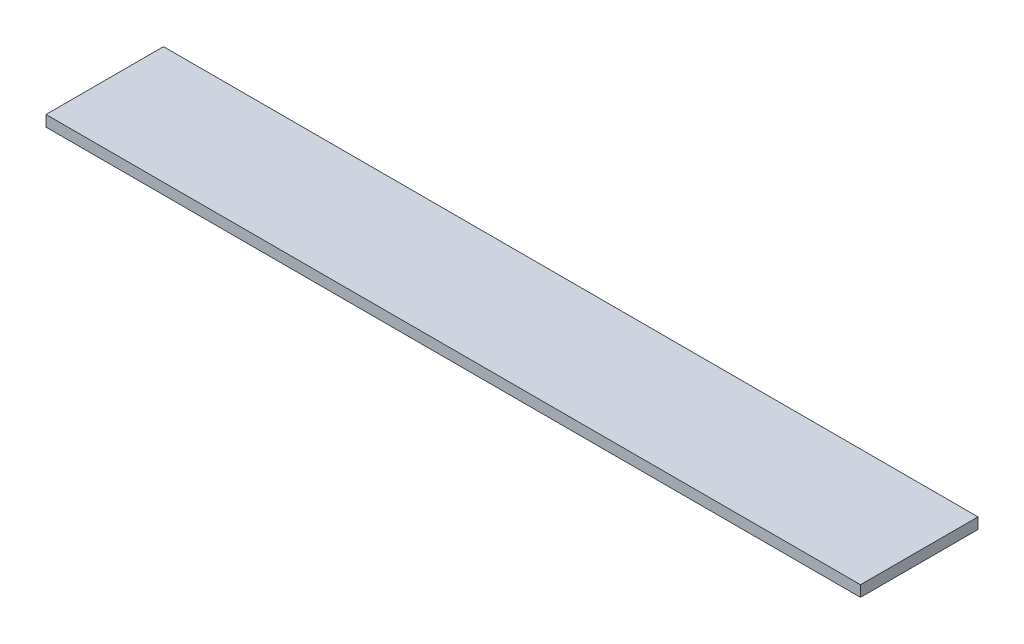
SolidWorks part; units mm, degrees
ref_plane "Front Plane" through (0, 0, 0) normal (0, 0, 1) x (1, 0, 0)
ref_plane "Top Plane" through (0, 0, 0) normal (0, 1, 0) x (1, 0, 0)
ref_plane "Right Plane" through (0, 0, 0) normal (1, 0, 0) x (0, 0, -1)
sketch "Sketch1" plane through (0, 0, 0) normal (0, 1, 0) x (1, 0, 0)
  line L1 (0, 0) -> (-222.5, 0)
  line L2 (0, 0) -> (0, 32.1)
  line L3 (0, 32.1) -> (-222.5, 32.1)
  line L4 (-222.5, 0) -> (-222.5, 32.1)
extrude "Boss-Extrude1" add sketch "Sketch1" along normal blind 3
